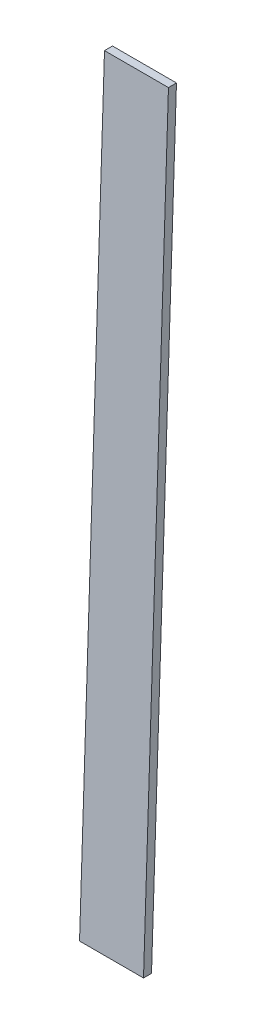
SolidWorks part; units mm, degrees
ref_plane "Front Plane" through (0, 0, 0) normal (0, 0, 1) x (1, 0, 0)
ref_plane "Top Plane" through (0, 0, 0) normal (0, 1, 0) x (1, 0, 0)
ref_plane "Right Plane" through (0, 0, 0) normal (1, 0, 0) x (0, 0, -1)
sketch "Sketch1" plane through (0, 0, 0) normal (0, 1, 0) x (1, 0, 0)
  line L1 (0, 0) -> (25.4, 0)
  line L2 (0, 0) -> (0, 3.175)
  line L3 (0, 3.175) -> (25.4, 3.175)
  line L4 (25.4, 0) -> (25.4, 3.175)
  dimension "D1" = 25.4
  dimension "D2" = 3.175
ref_plane "Plane1" through (0, 301.244, 0) normal (0, 1, 0) x (1, 0, 0)
sketch "Sketch2" plane through (0, 301.244, 0) normal (0, 1, 0) x (1, 0, 0)
  line L1 (0, 13.081) -> (25.4, 13.081)
  line L2 (0, 13.081) -> (0, 9.906)
  line L3 (0, 9.906) -> (25.4, 9.906)
  line L4 (25.4, 13.081) -> (25.4, 9.906)
  point P4 (2.1917, 9.906)
  point P6 (0, 0)
  dimension "D1" = 25.4
  dimension "D2" = 3.175
  dimension "D3" = 9.906
loft "Loft1" add profiles "Sketch2", "Sketch1"
